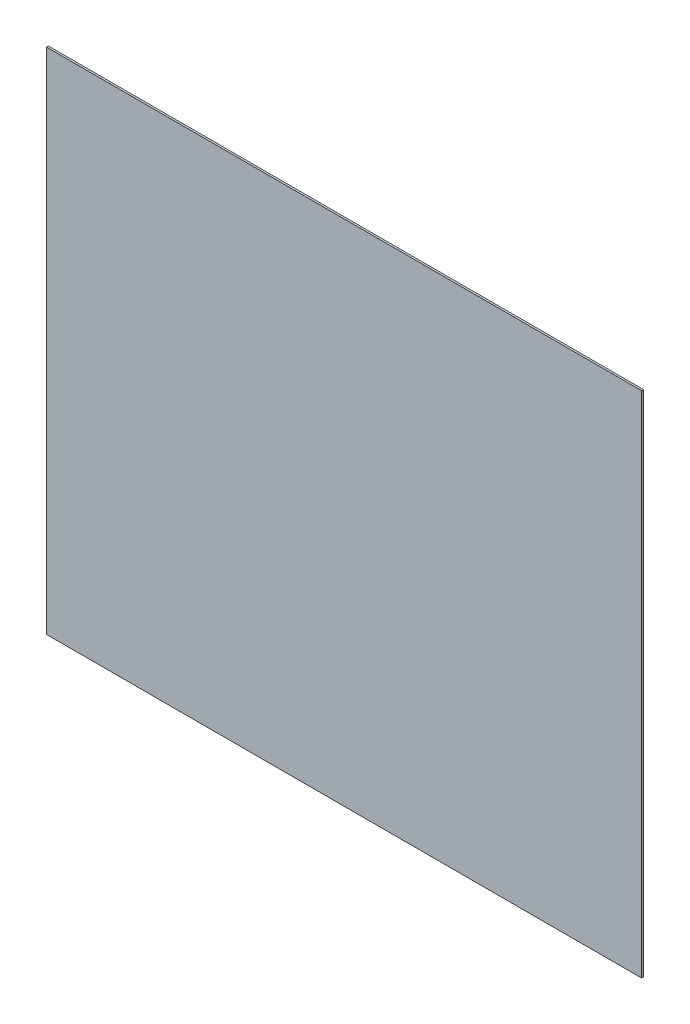
SolidWorks part; units mm, degrees
ref_plane "Front Plane" through (0, 0, 0) normal (0, 0, 1) x (1, 0, 0)
ref_plane "Top Plane" through (0, 0, 0) normal (0, 1, 0) x (1, 0, 0)
ref_plane "Right Plane" through (0, 0, 0) normal (1, 0, 0) x (0, 0, -1)
sketch "Sketch1" plane through (0, 0, 0) normal (0, 0, 1) x (1, 0, 0)
  line L0 (0, 0) -> (620, 0)
  line L1 (620, 0) -> (620, 530)
  line L2 (620, 530) -> (0, 530)
  line L3 (0, 530) -> (0, 0)
  line L4 (0, 0) -> (0.3678, -0.5517)
  dimension "D1" = 530
  dimension "D2" = 620
extrude "Boss-Extrude1" add sketch "Sketch1" along normal blind 2 contours L0 L1 L2 L3
